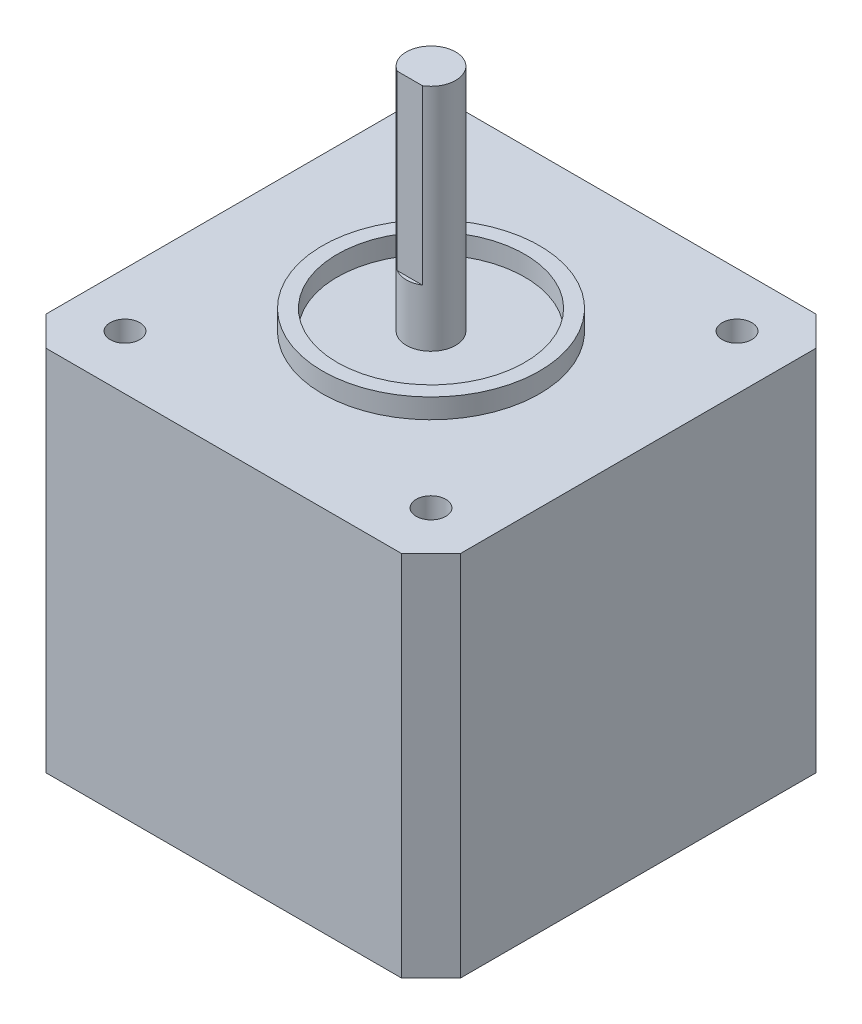
SolidWorks part; units mm, degrees
ref_plane "Front" through (0, 0, 0) normal (0, 0, 1) x (1, 0, 0)
ref_plane "Top" through (0, 0, 0) normal (0, 1, 0) x (1, 0, 0)
ref_plane "Right" through (0, 0, 0) normal (1, 0, 0) x (0, 0, -1)
sketch "Sketch1" plane through (0, 0, 0) normal (0, 1, 0) x (1, 0, 0)
  line L1 (-21, 21) -> (21, 21)
  line L2 (-21, 21) -> (-21, -21)
  line L3 (-21, -21) -> (21, -21)
  line L4 (21, 21) -> (21, -21)
  line L5 (-21, 21) -> (21, -21) construction
  line L6 (-21, -21) -> (21, 21) construction
  point P0 (0, 0)
  dimension "D1" = 42
  dimension "D2" = 42
extrude "Boss-Extrude1" add sketch "Sketch1" along normal blind 37.25
sketch "Sketch2" plane through (0, 37.25, 0) normal (0, 1, 0) x (1, 0, 0)
  line L1 (-15.5, 15.5) -> (15.5, 15.5) construction
  line L2 (-15.5, 15.5) -> (-15.5, -15.5) construction
  line L3 (-15.5, -15.5) -> (15.5, -15.5) construction
  line L4 (15.5, 15.5) -> (15.5, -15.5) construction
  line L5 (-15.5, 15.5) -> (15.5, -15.5) construction
  line L6 (-15.5, -15.5) -> (15.5, 15.5) construction
  circle A0 centre (15.5, 15.5) radius 1.5
  circle A1 centre (15.5, -15.5) radius 1.5
  circle A2 centre (-15.5, -15.5) radius 1.5
  circle A3 centre (-15.5, 15.5) radius 1.5
  point P0 (0, 0)
  dimension "D3" = 3
  dimension "D1" = 31
  dimension "D2" = 31
extrude "Cut-Extrude1" cut sketch "Sketch2" against normal blind 5
sketch "Sketch3" plane through (0, 37.25, 0) normal (0, 1, 0) x (1, 0, 0)
  circle A0 centre (0, 0) radius 11
  circle A1 centre (0, 0) radius 9.5
  dimension "D1" = 22
  dimension "D2" = 19
extrude "Boss-Extrude2" add sketch "Sketch3" along normal blind 2
ref_plane "Plane1" through (0, 60.5, 0) normal (0, 1, 0) x (1, 0, 0)
sketch "Sketch4" plane through (0, 60.5, 0) normal (0, 1, 0) x (1, 0, 0)
  line L0 (-1.2757, -2.15) -> (1.2757, -2.15)
  arc A0 (1.2757, -2.15) -> (-1.2757, -2.15) centre (0, 0) ccw
  dimension "D1" = 5
  dimension "D2" = 2.15
extrude "Boss-Extrude3" add sketch "Sketch4" against normal up to surface (23.25 mm away) separate body up to face at (0, 37.25, 9.5)
chamfer "Chamfer1" distance 3 4 edges at (-21, 18.625, 21) (-21, 18.625, -21) (21, 18.625, -21) (21, 18.625, 21)
sketch "Sketch6" plane through (0, 0, 0) normal (0, -1, 0) x (1, 0, 0)
  circle A0 centre (0, 0) radius 4.5
  dimension "D1" = 9
extrude "Cut-Extrude2" cut sketch "Sketch6" against normal blind 3.25
sketch "Sketch7" plane through (0, 37.25, 0) normal (0, 1, 0) x (1, 0, 0)
  circle A0 centre (0, 0) radius 2.5
extrude "Boss-Extrude4" add sketch "Sketch7" along normal offset from surface (5.75 mm away) 17.5 up to face at (0, 60.5, -0.175)
